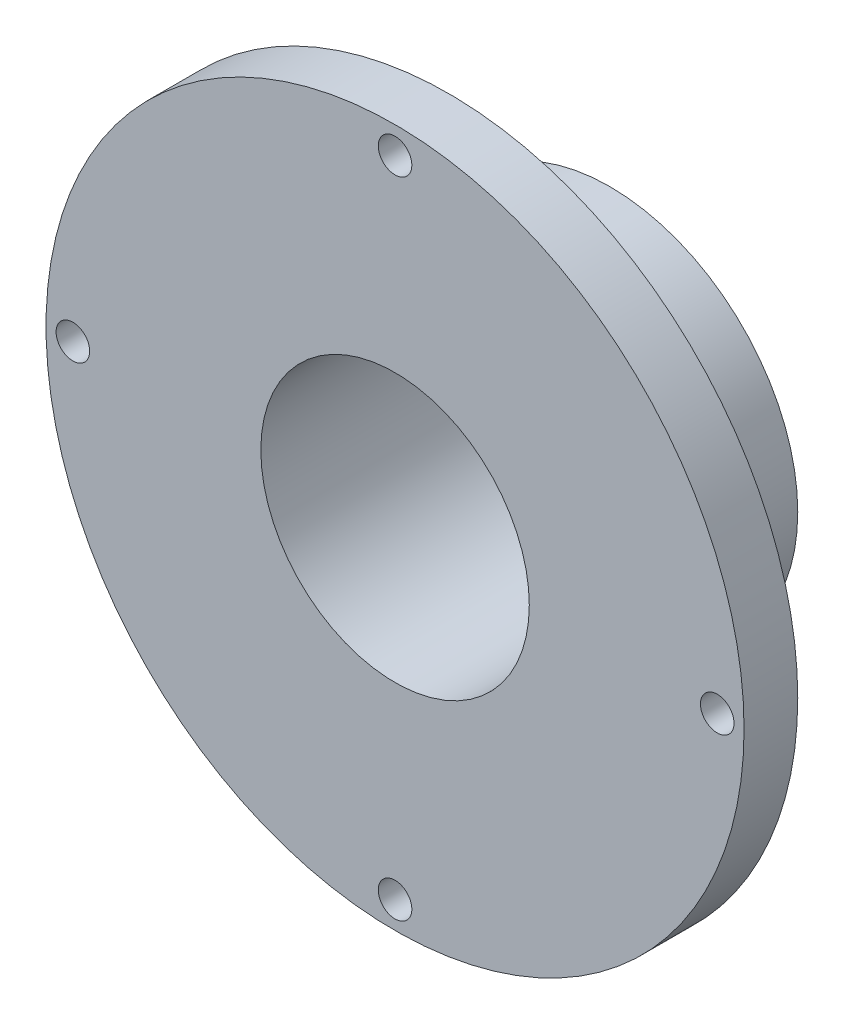
SolidWorks part; units mm, degrees
ref_plane "Front Plane" through (0, 0, 0) normal (0, 0, 1) x (1, 0, 0)
ref_plane "Top Plane" through (0, 0, 0) normal (0, 1, 0) x (1, 0, 0)
ref_plane "Right Plane" through (0, 0, 0) normal (1, 0, 0) x (0, 0, -1)
sketch "Sketch1" plane through (0, 0, 0) normal (0, 0, 1) x (1, 0, 0)
  circle A0 centre (0, 0) radius 41.275
  dimension "D1" = 82.55
extrude "Boss-Extrude1" add sketch "Sketch1" along normal blind 25.4
sketch "Sketch2" plane through (0, 0, 0) normal (0, 0, -1) x (-1, 0, 0)
  circle A0 centre (0, 0) radius 22.225
  dimension "D1" = 44.45
extrude "Cut-Extrude1" cut sketch "Sketch2" against normal offset from surface (19.05 mm away) 19.05 flip side to cut up to plane "Front Plane"
sketch "Sketch3" plane through (0, 0, 0) normal (0, 0, -1) x (-1, 0, 0)
  circle A0 centre (0, 0) radius 15.875
  dimension "D1" = 31.75
extrude "Cut-Extrude2" cut sketch "Sketch3" against normal through all
hole_wizard "#4-40 Tapped Hole1" positions "Sketch8" profile "Sketch7" tap size "#4-40" standard "ANSI Inch"
sketch "Sketch8" plane through (0, 0, 0) normal (0, 0, -1) x (-1, 0, 0)
  point P0 (0, 18.415)
  point P4 (0, -18.415)
  dimension "D1" = 18.415
  dimension "D2" = 18.415
sketch "Sketch7" plane through (0, 18.415, 0) normal (1, 0, 0) x (0, 1, 0)
  line L0 (0, 0) -> (0, 8.2738)
  line L1 (0, 8.2738) -> (1.1303, 7.5946)
  line L2 (1.1303, 7.5946) -> (1.1303, 0)
  line L5 (1.1303, 0) -> (0, 0)
  line L10 (0, 8.2738) -> (-1.1303, 7.5946) construction
  line L11 (0, -6.35) -> (0, 107.95) construction
  dimension "Tap Drill Dia." = 2.2606
  dimension "Tap Drill Depth" = 7.5946
  dimension "Drill Angle" = 118
hole_wizard "5/32 (0.15625) Diameter Hole1" positions "Sketch5" profile "Sketch6" hole size "5/32" standard "ANSI Inch" end condition through all
sketch "Sketch5" plane through (0, 0, 25.4) normal (0, 0, 1) x (1, 0, 0)
  point P0 (0, 38.1)
  point P2 (38.1, 0)
  dimension "D1" = 38.1
  dimension "D2" = 38.1
sketch "Sketch6" plane through (0, 38.1, 25.4) normal (1, 0, 0) x (0, -1, 0)
  line L0 (0, 0) -> (0, 25.4)
  line L1 (0, 25.4) -> (1.9844, 25.4)
  line L2 (1.9844, 25.4) -> (1.9844, 0)
  line L5 (1.9844, 0) -> (0, 0)
  line L11 (0, -6.35) -> (0, 107.95) construction
  dimension "Thru Hole Dia." = 3.9688
  dimension "Thru Hole Depth" = 25.4
mirror "Mirror1" about plane through (0, 0, 0) normal (0, 1, 0) of "5/32 (0.15625) Diameter Hole1"
mirror "Mirror2" about plane through (0, 0, 0) normal (1, 0, 0) of "Mirror1"
equation "\"D2@Sketch8\"=\"D1@Sketch8\""
equation "\"D1@Sketch8\"=\"D1@Sketch3\"/2+0.1"
